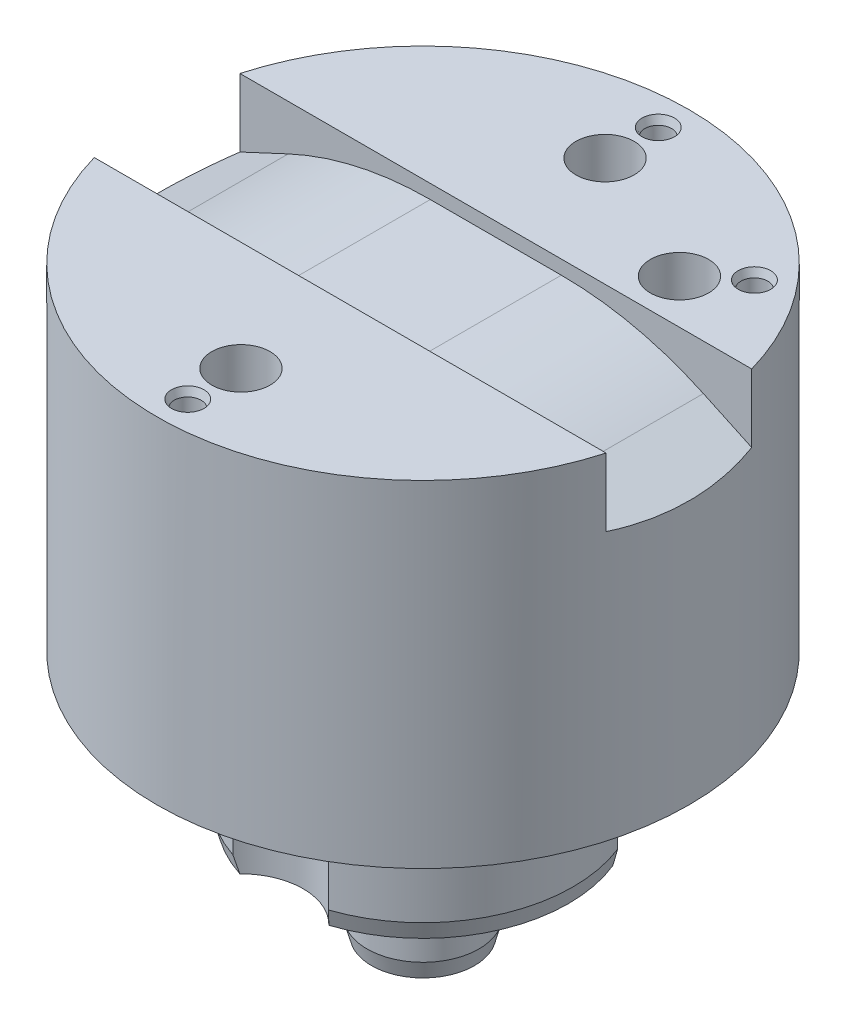
SolidWorks part; units mm, degrees
ref_plane "Front Plane" through (0, 0, 0) normal (0, 0, 1) x (1, 0, 0)
ref_plane "Top Plane" through (0, 0, 0) normal (0, 1, 0) x (1, 0, 0)
ref_plane "Right Plane" through (0, 0, 0) normal (1, 0, 0) x (0, 0, -1)
sketch "Sketch1" plane through (0, 0, 0) normal (0, 0, 1) x (1, 0, 0)
  line L0 (0, 0) -> (0, 50000) construction
  line L2 (5, -22) -> (5, -13)
  line L3 (5, -13) -> (13.4, -13)
  line L4 (13.4, -13) -> (13.4, 0)
  line L5 (13.4, 0) -> (23.75, 0)
  line L6 (23.75, 0) -> (23.75, 30)
  line L7 (23.75, 30) -> (0, 30)
  line L9 (5, -22) -> (0, -22)
  line L10 (0, -22) -> (0, 30)
  dimension "D1" = 10
  dimension "D2" = 26.8
  dimension "D3" = 47.5
  dimension "D4" = 9
  dimension "D5" = 13
  dimension "D6" = 30
revolve "Revolve1" add sketch "Sketch1" angle 360 about L0
sketch "Sketch12" plane through (0, 0, 0) normal (0, 1, 0) x (1, 0, 0)
  line L0 (0, 0) -> (12.4482, 10.4453) construction
  line L1 (0, 0) -> (0, 16.25) construction
  line L2 (0, 16.25) -> (0, 21) construction
  line L3 (0, 0) -> (0, -16.25) construction
  line L4 (0, -16.25) -> (0, -21) construction
  line L5 (12.4482, 10.4453) -> (16.0869, 13.4985) construction
  circle A0 centre (0, 0) radius 16.25 construction
  circle A1 centre (0, 0) radius 21 construction
  point P3 (0, -16.25)
  point P4 (0, 16.25)
  point P5 (12.4482, 10.4453)
  point P14 (0, 21)
  point P15 (16.0869, 13.4985)
  point P16 (0, -21)
  dimension "D1" = 32.5
  dimension "D3" = 4.75
  dimension "D2" = 50
chamfer "Chamfer2" distance 0.4 angle 75 2 edges at (0, -22, -5) (0, -13, -13.4)
hole_wizard "CBORE for M5 SBHCS1" positions "Sketch13" profile "Sketch15" counterbore size "M5" standard "ANSI Metric"
sketch "Sketch13" plane through (0, 0, 0) normal (0, -1, 0) x (-1, 0, 0)
  point P0 (0, -16.25)
  point P3 (0, 16.25)
  point P6 (-12.4482, 10.4453)
sketch "Sketch15" plane through (0, 0, 16.25) normal (1, 0, 0) x (0, 0, -1)
  line L0 (0, 0) -> (0, 30)
  line L1 (0, 30) -> (2.6, 30)
  line L3 (2.6, 30) -> (2.6, 24)
  line L4 (2.6, 24) -> (5.55, 24)
  line L5 (5.55, 24) -> (5.55, 0)
  line L7 (5.55, 0) -> (0, 0)
  line L11 (0, -6.35) -> (0, 107.95) construction
  dimension "Thru Hole Dia." = 5.2
  dimension "Thru Hole Depth" = 30
  dimension "C'Bore Dia." = 11.1
  dimension "C'Bore Depth" = 24
sketch "Sketch16" plane through (0, 0, 0) normal (0, -1, 0) x (1, 0, 0)
  arc A0 (-4.2679, -12.7022) -> (4.2679, -12.7022) centre (0, -16.25) ccw construction
  arc A1 (6.987, -11.4342) -> (12.4738, -4.8954) centre (12.4482, -10.4453) ccw construction
  arc A2 (4.2679, 12.7022) -> (-4.2679, 12.7022) centre (0, 16.25) ccw construction
  circle A3 centre (0, -16.25) radius 5.55
  circle A4 centre (12.4482, -10.4453) radius 5.55
  circle A5 centre (0, 16.25) radius 5.55
extrude "Cut-Extrude6" cut sketch "Sketch16" along normal through all
hole_wizard "Ø2.4 (2.4) Diameter Hole1" positions "Sketch17" profile "Sketch19" hole size "Ø2.4" standard "ANSI Metric"
sketch "Sketch17" plane through (0, 30, 0) normal (0, 1, 0) x (1, 0, 0)
  point P0 (0, 21)
  point P3 (16.0869, 13.4985)
  point P6 (0, -21)
sketch "Sketch19" plane through (0, 30, -21) normal (1, 0, 0) x (0, 0, 1)
  line L0 (0, 0) -> (0, 2)
  line L1 (0, 2) -> (1.2, 2)
  line L2 (1.2, 2) -> (1.2, 0)
  line L5 (1.2, 0) -> (0, 0)
  line L10 (0, 2) -> (-1.2, 2) construction
  line L11 (0, -6.35) -> (0, 107.95) construction
  dimension "Hole Dia." = 2.4
  dimension "Hole Depth" = 2
  dimension "Drill Angle" = 180
chamfer "Chamfer1" distance 0.25 angle 70 3 edges at (0, 30, 22.2) (16.0869, 30, -12.2985) (0, 30, -19.8)
ref_plane "Plane1" [suppressed] through (0, 28.8, 0) normal (0, 1, 0) x (1, 0, 0)
sketch "Sketch31" [suppressed] plane through (0, 28.8, 0) normal (0, 1, 0) x (1, 0, 0)
  circle A0 centre (0, 0) radius 23.75
  circle A1 centre (0, 0) radius 23.75 construction
extrude "Cut-Extrude9" [suppressed] cut sketch "Sketch31" against normal through all
sketch "Sketch30" plane through (0, 0, 0) normal (0, 0, 1) x (1, 0, 0)
  line L0 (-23.75, 30) -> (23.75, 30)
  line L1 (23.75, 30) -> (23.75, 23.504)
  line L2 (23.75, 0) -> (23.75, 30) construction
  line L3 (23.75, 23.504) -> (12.5, 28.75)
  line L4 (12.5, 28.75) -> (-12.5, 28.75)
  line L5 (-12.5, 28.75) -> (-23.75, 23.504)
  line L6 (-23.75, 30) -> (-23.75, 0) construction
  line L7 (-23.75, 23.504) -> (-23.75, 30)
  point P12 (0, 28.75)
  dimension "D1" = 1.25
  dimension "D2" = 155
  dimension "D3" = 25
extrude "Cut-Extrude8" cut sketch "Sketch30" against normal mid plane 13
fillet "Fillet1" radius 30 2 edges at (12.5, 28.75, 0) (-12.5, 28.75, 0)
